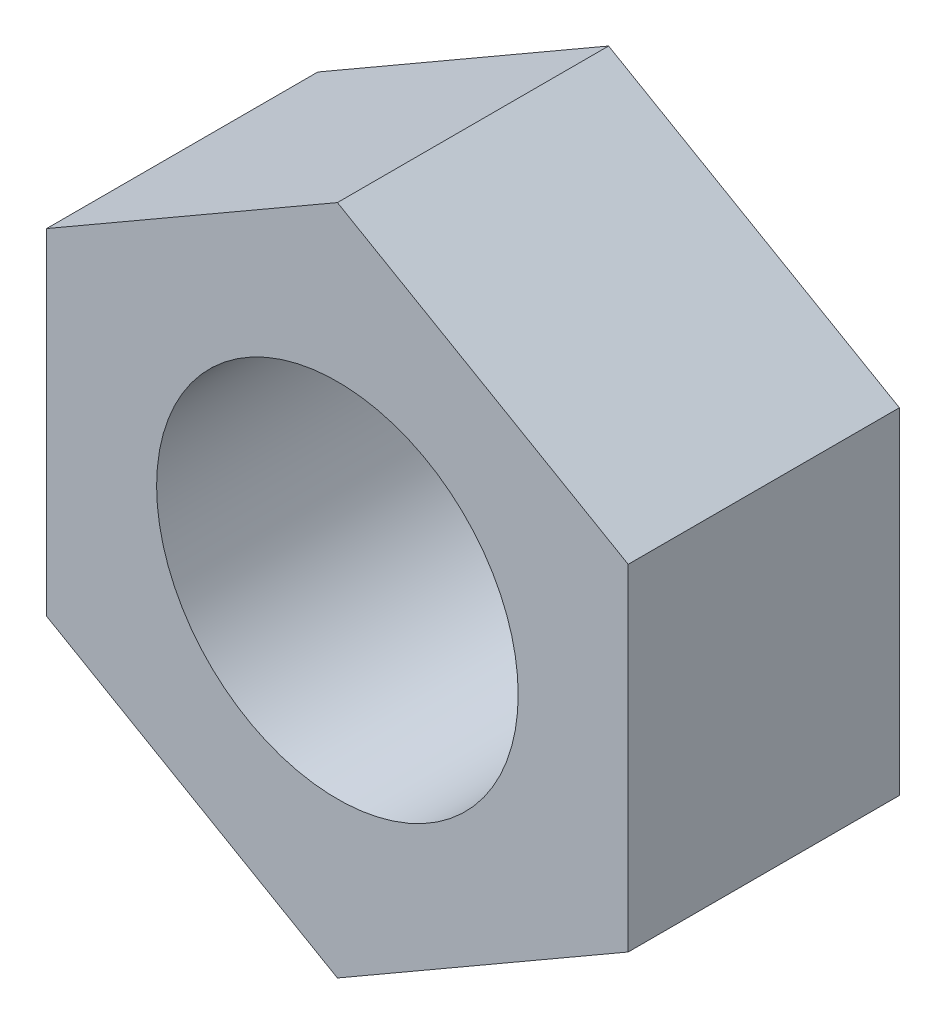
SolidWorks part; units mm, degrees
ref_plane "Front Plane" through (0, 0, 0) normal (0, 0, 1) x (1, 0, 0)
ref_plane "Top Plane" through (0, 0, 0) normal (0, 1, 0) x (1, 0, 0)
ref_plane "Right Plane" through (0, 0, 0) normal (1, 0, 0) x (0, 0, -1)
sketch "Sketch1" plane through (0, 0, 0) normal (0, 0, 1) x (1, 0, 0)
  line L1 (0, 11.1429) -> (-9.65, 5.5714)
  line L2 (-9.65, 5.5714) -> (-9.65, -5.5714)
  line L3 (-9.65, -5.5714) -> (0, -11.1429)
  line L4 (0, -11.1429) -> (9.65, -5.5714)
  line L5 (9.65, -5.5714) -> (9.65, 5.5714)
  line L6 (9.65, 5.5714) -> (0, 11.1429)
  circle A0 centre (0, 0) radius 9.65 construction
  circle A1 centre (0, 0) radius 6
  point P10 (0, 0)
  dimension "D2" = 12
  dimension "D1" = 19.3
extrude "Boss-Extrude1" add sketch "Sketch1" along normal mid plane 9
